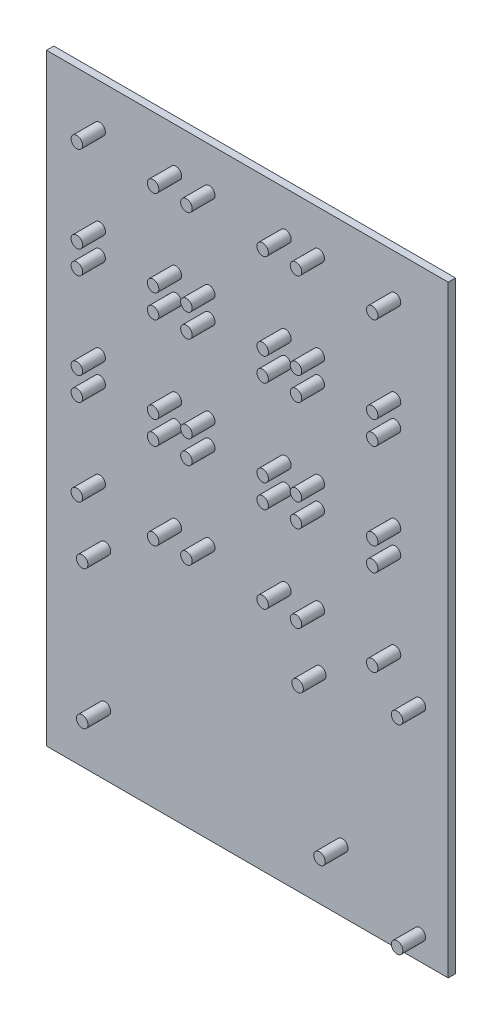
SolidWorks part; units mm, degrees
ref_plane "Front Plane" through (0, 0, 0) normal (0, 0, 1) x (1, 0, 0)
ref_plane "Top Plane" through (0, 0, 0) normal (0, 1, 0) x (1, 0, 0)
ref_plane "Right Plane" through (0, 0, 0) normal (1, 0, 0) x (0, 0, -1)
sketch "Sketch1" plane through (0, 0, 0) normal (0, 0, 1) x (1, 0, 0)
  line L1 (-69.85, -104.775) -> (69.85, -104.775)
  line L2 (-69.85, -104.775) -> (-69.85, 104.775)
  line L3 (-69.85, 104.775) -> (69.85, 104.775)
  line L4 (69.85, -104.775) -> (69.85, 104.775)
  line L5 (-69.85, -104.775) -> (69.85, 104.775) construction
  line L6 (-69.85, 104.775) -> (69.85, -104.775) construction
  point P0 (0, 0)
  dimension "D1" = 209.55
  dimension "D2" = 139.7
extrude "Boss-Extrude1" add sketch "Sketch1" along normal blind 2.54
sketch "Sketch2" plane through (0, 0, 2.54) normal (0, 0, 1) x (1, 0, 0)
  line L0 (-69.85, 104.775) -> (-69.85, -104.775) construction
  line L2 (-69.85, -104.775) -> (69.85, -104.775) construction
  circle A0 centre (-51.35, 14.125) radius 2
  circle A1 centre (-24.85, 14.125) radius 2
  circle A2 centre (-24.85, -15.875) radius 2
  circle A3 centre (-51.35, -15.875) radius 2
  circle A4 centre (13.25, 14.125) radius 2
  circle A5 centre (-13.25, 14.125) radius 2
  circle A6 centre (-13.25, -15.875) radius 2
  circle A7 centre (13.25, -15.875) radius 2
  circle A8 centre (51.35, 14.125) radius 2
  circle A9 centre (24.85, 14.125) radius 2
  circle A10 centre (24.85, -15.875) radius 2
  circle A11 centre (51.35, -15.875) radius 2
  circle A12 centre (13.25, 52.225) radius 2
  circle A13 centre (-13.25, 52.225) radius 2
  circle A14 centre (-13.25, 22.225) radius 2
  circle A15 centre (13.25, 22.225) radius 2
  circle A16 centre (51.35, 52.225) radius 2
  circle A17 centre (24.85, 52.225) radius 2
  circle A18 centre (24.85, 22.225) radius 2
  circle A19 centre (51.35, 22.225) radius 2
  circle A20 centre (13.25, 90.325) radius 2
  circle A21 centre (-13.25, 90.325) radius 2
  circle A22 centre (-13.25, 60.325) radius 2
  circle A23 centre (13.25, 60.325) radius 2
  circle A24 centre (51.35, 90.325) radius 2
  circle A25 centre (24.85, 90.325) radius 2
  circle A26 centre (24.85, 60.325) radius 2
  circle A27 centre (51.35, 60.325) radius 2
  circle A28 centre (-24.85, 52.225) radius 2
  circle A29 centre (-51.35, 52.225) radius 2
  circle A30 centre (-51.35, 22.225) radius 2
  circle A31 centre (-24.85, 22.225) radius 2
  circle A32 centre (-24.85, 90.325) radius 2
  circle A33 centre (-51.35, 90.325) radius 2
  circle A34 centre (-51.35, 60.325) radius 2
  circle A35 centre (-24.85, 60.325) radius 2
  dimension "D5" = 4
  dimension "D6" = 4
  dimension "D8" = 4
  dimension "D9" = 4
  dimension "D2" = 18.5
  dimension "D3" = 18.5
  dimension "D4" = 88.9
  dimension "D7" = 26.5
  dimension "D10" = 30
  dimension "D11" = 30
  dimension "D12" = 26.5
  dimension "D13" = 88.9
  dimension "D14" = 3
  dimension "D15" = 3
sketch "Sketch3" plane through (0, 0, 2.54) normal (0, 0, 1) x (1, 0, 0)
  line L0 (-69.85, 104.775) -> (-69.85, -104.775) construction
  line L1 (-63.5, -85.725) -> (38.1, -85.725)
  line L2 (-63.5, -85.725) -> (-63.5, -32.385)
  line L3 (-63.5, -32.385) -> (38.1, -32.385)
  line L4 (38.1, -85.725) -> (38.1, -32.385)
  line L5 (-63.5, -85.725) -> (38.1, -32.385) construction
  line L6 (-63.5, -32.385) -> (38.1, -85.725) construction
  line L7 (-69.85, -104.775) -> (69.85, -104.775) construction
  line L8 (69.85, -104.775) -> (69.85, 104.775) construction
  line L9 (44.45, -100.0125) -> (63.5, -100.0125)
  line L10 (44.45, -100.0125) -> (44.45, -23.8125)
  line L11 (44.45, -23.8125) -> (63.5, -23.8125)
  line L12 (63.5, -100.0125) -> (63.5, -23.8125)
  line L13 (44.45, -100.0125) -> (63.5, -23.8125) construction
  line L14 (44.45, -23.8125) -> (63.5, -100.0125) construction
  circle A0 centre (-49.5, -83.225) radius 2
  circle A1 centre (-49.5, -35.025) radius 2
  circle A2 centre (25.4, -35.025) radius 2
  circle A3 centre (33.02, -83.225) radius 2
  circle A4 centre (60, -27.3125) radius 2
  circle A5 centre (60, -96.5125) radius 2
  point P0 (-12.7, -59.055)
  point P9 (53.975, -61.9125)
  dimension "D10" = 2.5
  dimension "D11" = 4
  dimension "D13" = 48.2
  dimension "D14" = 4
  dimension "D16" = 4
  dimension "D17" = 0
  dimension "D18" = 96.52
  dimension "D20" = 2.5
  dimension "D19" = 4
  dimension "D21" = 3.5
  dimension "D22" = 3.5
  dimension "D23" = 4
  dimension "D24" = 3.5
  dimension "D25" = 3.5
  dimension "D26" = 4
  dimension "D1" = 6.35
  dimension "D2" = 101.6
  dimension "D3" = 53.34
  dimension "D4" = 19.05
  dimension "D5" = 19.05
  dimension "D6" = 76.2
  dimension "D7" = 4.7625
  dimension "D8" = 6.35
  dimension "D9" = 14
  dimension "D12" = 14
  dimension "D15" = 74.9
extrude "Boss-Extrude2" add sketch "Sketch2" along normal blind 7.9375
extrude "Boss-Extrude3" add sketch "Sketch3" along normal blind 7.9375 contours A0 | A3 | A5 | A4 | A2 | A1
